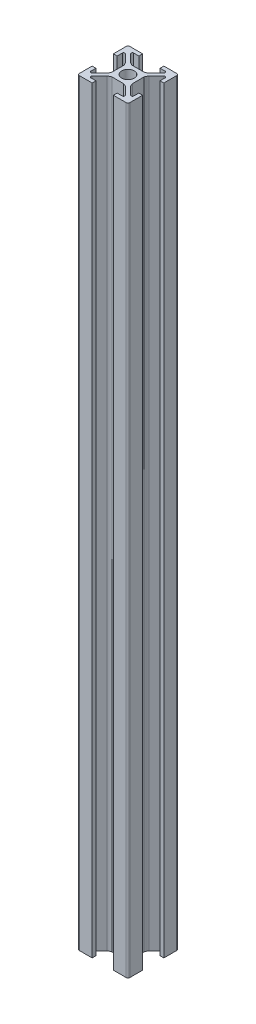
SolidWorks part; units mm, degrees
ref_plane "Front Plane" through (0, 0, 0) normal (0, 0, 1) x (1, 0, 0)
ref_plane "Top Plane" through (0, 0, 0) normal (0, 1, 0) x (1, 0, 0)
ref_plane "Right Plane" through (0, 0, 0) normal (1, 0, 0) x (0, 0, -1)
sketch "Sketch1" plane through (0, 0, 0) normal (0, 1, 0) x (1, 0, 0)
  line L0 (-3.611, 4.6716) -> (-6.5858, 7.6464)
  line L1 (9.25, -10) -> (4.2, -10)
  line L2 (10, -9.25) -> (10, -4.2)
  line L3 (9.25, 10) -> (4.2, 10)
  line L4 (-10, -9.25) -> (-10, -4.2)
  line L5 (10, -10) -> (-10, 10) construction
  line L6 (10, 10) -> (-10, -10) construction
  line L7 (2.2681, -4) -> (-2.2681, -4)
  line L8 (4, -2.2681) -> (4, 2.2681)
  line L9 (2.2681, 4) -> (-2.2681, 4)
  line L10 (-4, -2.2681) -> (-4, 2.2681)
  line L11 (4, -4) -> (-4, 4) construction
  line L12 (4, 4) -> (-4, -4) construction
  line L13 (-6.2322, 8.5) -> (-4.2, 8.5)
  line L14 (-4.2, 8.5) -> (-4.2, 10)
  line L15 (4.6716, 3.611) -> (7.6464, 6.5858)
  line L16 (8.5, 6.2322) -> (8.5, 4.2)
  line L17 (8.5, 4.2) -> (10, 4.2)
  line L18 (4.2, 8.5) -> (4.2, 10)
  line L19 (-8.5, 4.2) -> (-10, 4.2)
  line L20 (-8.5, 6.2322) -> (-8.5, 4.2)
  line L21 (-4.6716, 3.611) -> (-7.6464, 6.5858)
  line L22 (0, 10) -> (0, -10) construction
  line L23 (6.2322, 8.5) -> (4.2, 8.5)
  line L24 (3.611, 4.6716) -> (6.5858, 7.6464)
  line L25 (-55, 0) -> (55, 0) construction
  line L26 (3.611, -4.6716) -> (6.5858, -7.6464)
  line L27 (6.2322, -8.5) -> (4.2, -8.5)
  line L28 (-4.6716, -3.611) -> (-7.6464, -6.5858)
  line L29 (-8.5, -6.2322) -> (-8.5, -4.2)
  line L30 (-8.5, -4.2) -> (-10, -4.2)
  line L31 (4.2, -8.5) -> (4.2, -10)
  line L32 (8.5, -4.2) -> (10, -4.2)
  line L33 (8.5, -6.2322) -> (8.5, -4.2)
  line L34 (4.6716, -3.611) -> (7.6464, -6.5858)
  line L35 (-4.2, -8.5) -> (-4.2, -10)
  line L36 (-6.2322, -8.5) -> (-4.2, -8.5)
  line L37 (2.2681, -4) -> (-2.2681, -4)
  line L38 (10, -10) -> (4.2, -10)
  line L39 (-3.611, -4.6716) -> (-6.5858, -7.6464)
  line L40 (-4.2, 10) -> (-9.25, 10)
  line L41 (-10, 4.2) -> (-10, 9.25)
  line L42 (-4.2, -10) -> (-9.25, -10)
  line L43 (-4.2, -10) -> (-10, -10)
  line L44 (10, 4.2) -> (10, 9.25)
  circle A0 centre (0, 0) radius 2.5
  arc A1 (-8.5, 6.2322) -> (-7.6464, 6.5858) centre (-8, 6.2322) cw
  arc A2 (-6.5858, 7.6464) -> (-6.2322, 8.5) centre (-6.2322, 8) cw
  arc A3 (-3.611, 4.6716) -> (-2.2681, 4) centre (-1.7294, 6.7555) ccw
  arc A4 (-4.6716, 3.611) -> (-4, 2.2681) centre (-6.7555, 1.7294) cw
  arc A5 (4.6716, 3.611) -> (4, 2.2681) centre (6.7555, 1.7294) ccw
  arc A6 (3.611, 4.6716) -> (2.2681, 4) centre (1.7294, 6.7555) cw
  arc A7 (6.5858, 7.6464) -> (6.2322, 8.5) centre (6.2322, 8) ccw
  arc A8 (8.5, 6.2322) -> (7.6464, 6.5858) centre (8, 6.2322) ccw
  arc A9 (8.5, -6.2322) -> (7.6464, -6.5858) centre (8, -6.2322) cw
  arc A10 (6.5858, -7.6464) -> (6.2322, -8.5) centre (6.2322, -8) cw
  arc A11 (3.611, -4.6716) -> (2.2681, -4) centre (1.7294, -6.7555) ccw
  arc A12 (4.6716, -3.611) -> (4, -2.2681) centre (6.7555, -1.7294) cw
  arc A13 (-4.6716, -3.611) -> (-4, -2.2681) centre (-6.7555, -1.7294) ccw
  arc A14 (-3.611, -4.6716) -> (-2.2681, -4) centre (-1.7294, -6.7555) cw
  arc A15 (-6.5858, -7.6464) -> (-6.2322, -8.5) centre (-6.2322, -8) ccw
  arc A16 (-8.5, -6.2322) -> (-7.6464, -6.5858) centre (-8, -6.2322) ccw
  arc A17 (-9.25, -10) -> (-10, -9.25) centre (-9.25, -9.25) cw
  arc A18 (9.25, -10) -> (10, -9.25) centre (9.25, -9.25) ccw
  arc A19 (10, 9.25) -> (9.25, 10) centre (9.25, 9.25) ccw
  arc A20 (-9.25, 10) -> (-10, 9.25) centre (-9.25, 9.25) ccw
  point P0 (0, 0)
  point P18 (-8.5, 7.4393)
  point P24 (-7.4393, 8.5)
  point P50 (7.4393, 8.5)
  point P51 (8.5, 7.4393)
  point P86 (8.5, -7.4393)
  point P87 (7.4393, -8.5)
  point P88 (-7.4393, -8.5)
  point P89 (-8.5, -7.4393)
  dimension "D2" = 5
  dimension "D7" = 0.5
  dimension "D8" = 0.75
  dimension "D1" = 20
  dimension "D3" = 8
  dimension "D4" = 1.5
  dimension "D5" = 1.5
  dimension "D6" = 8.4
extrude "Boss-Extrude1" add sketch "Sketch1" along normal blind 300 contours L40 A20 L41 L19 L20 A1 L21 A4 L10 A13 L28 A16 L29 L30 L4 A17 L42 L35 L36 A15 L39 A14 L7 A11 L26 A10 L27 L31 L1 A18 L2 L32 L33 A9 L34 A12 L8 A5 L15 A8 L16 L17 L44 A19 L3 L18 L23 A7 L24 A6 L9
